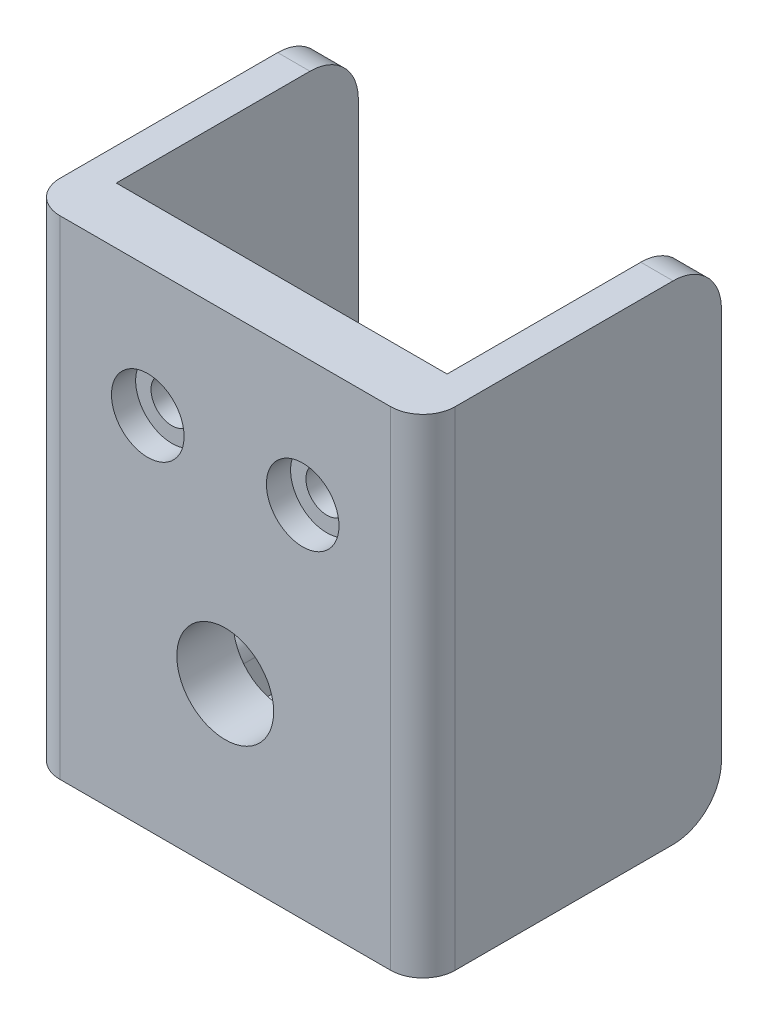
SolidWorks part; units mm, degrees
ref_plane "Front Plane" through (0, 0, 0) normal (0, 0, 1) x (1, 0, 0)
ref_plane "Top Plane" through (0, 0, 0) normal (0, 1, 0) x (1, 0, 0)
ref_plane "Right Plane" through (0, 0, 0) normal (1, 0, 0) x (0, 0, -1)
sketch "Sketch1" plane through (0, 0, 0) normal (0, 0, 1) x (1, 0, 0)
  line L0 (-10.25, 13) -> (10.25, 13)
  line L1 (-10.25, 13) -> (-10.25, -17.25)
  line L2 (-10.25, -17.25) -> (10.25, -17.25)
  line L3 (10.25, 13) -> (10.25, -17.25)
  line L4 (-4.8, 5) -> (4.8, 5) construction
  line L5 (0, -7) -> (0, -17.25) construction
  line L6 (0, 13) -> (0, 5) construction
  line L7 (0, 5) -> (0, 0) construction
  line L8 (0, 0) -> (0, -7) construction
  circle A1 centre (-4.8, 5) radius 1.3
  circle A2 centre (4.8, 5) radius 1.3
  circle A3 centre (0, -7) radius 3
  point P14 (0, 5)
  dimension "D3" = 2.6
  dimension "D4" = 6
  dimension "D1" = 30.25
  dimension "D2" = 20.5
  dimension "D5" = 10.25
  dimension "D6" = 8
  dimension "D7" = 9.6
  dimension "D8" = 7
extrude "Boss-Extrude1" add sketch "Sketch1" along normal blind 3.5
sketch "Sketch2" plane through (0, -17.25, 0) normal (0, -1, 0) x (-1, 0, 0)
  line L1 (10.25, -3.5) -> (12.25, -3.5)
  line L2 (10.25, -3.5) -> (10.25, 15)
  line L3 (10.25, 15) -> (12.25, 15)
  line L4 (12.25, -3.5) -> (12.25, 15)
  line L5 (-10.25, -3.5) -> (-12.25, -3.5)
  line L6 (-10.25, -3.5) -> (-10.25, 15)
  line L7 (-10.25, 15) -> (-12.25, 15)
  line L8 (-12.25, -3.5) -> (-12.25, 15)
  dimension "D1" = 2
  dimension "D2" = 18.5
extrude "Boss-Extrude2" add sketch "Sketch2" against normal up to vertex (30.25 mm away)
sketch "Sketch3" plane through (0, -17.25, 0) normal (0, -1, 0) x (1, 0, 0)
  line L0 (0, 3.5) -> (0, 0) construction
  line L5 (-12.25, 3.5) -> (12.25, 3.5) construction
  line L6 (0, 0) -> (0, -15.097) construction
  line L11 (-3.75, -10.5) -> (3.75, -10.5) construction
  line L12 (-10.25, 0) -> (-3.75, 0)
  line L13 (-10.25, 0) -> (-10.25, -10.5)
  line L14 (-10.25, -10.5) -> (-3.75, -10.5)
  line L15 (-3.75, 0) -> (-3.75, -10.5)
  line L16 (10.25, 0) -> (3.75, 0)
  line L17 (10.25, 0) -> (10.25, -10.5)
  line L18 (10.25, -10.5) -> (3.75, -10.5)
  line L19 (3.75, 0) -> (3.75, -10.5)
  point P15 (0, -10.5)
  dimension "D1" = 10.5
  dimension "D3" = 7.5
extrude "Boss-Extrude3" add sketch "Sketch3" against normal blind 2
fillet "Fillet1" radius 3.5 2 edges at (3.75, -16.25, 0) (-3.75, -16.25, 0)
fillet "Fillet2" radius 2 2 edges at (-12.25, -2.125, 3.5) (12.25, -2.125, 3.5)
sketch "Sketch4" plane through (0, 0, 3.5) normal (0, 0, 1) x (1, 0, 0)
  circle A0 centre (-4.8, 5) radius 2.25
  circle A1 centre (4.8, 5) radius 2.25
  dimension "D1" = 4.5
extrude "Cut-Extrude1" cut sketch "Sketch4" against normal blind 1.5
fillet "Fillet4" radius 3 4 edges at (11.25, 13, -15) (-11.25, 13, -15) (-11.25, -17.25, -15) (11.25, -17.25, -15)
sketch "Sketch7" [suppressed] plane through (12.25, 0, 0) normal (1, 0, 0) x (0, 0, -1)
  line L0 (-1.0366, -17.25) -> (-1.0366, -7.25) construction
  line L1 (12, -17.25) -> (-1.5, -17.25) construction
  line L2 (0.7746, -7.25) -> (-1.0366, -7.25) construction
  line L4 (4.2746, -7.25) -> (16.1029, -7.25) construction
  line L5 (4.2746, -3.75) -> (16.1029, -3.75) construction
  line L6 (4.2746, -10.75) -> (16.1029, -10.75) construction
  arc A0 (4.2746, -3.75) -> (4.2746, -10.75) centre (4.2746, -7.25) ccw construction
  arc A1 (16.1029, -10.75) -> (16.1029, -3.75) centre (16.1029, -7.25) ccw construction
  point P9 (10.1887, -7.25)
  dimension "D1" = 3.5
  dimension "D2" = 10
extrude "Cut-Extrude4" [suppressed] cut sketch "Sketch7" against normal blind 10
fillet "Fillet5" [suppressed] radius 1.5
sketch "Sketch9" plane through (0, 0, 0) normal (0, 0, -1) x (-1, 0, 0)
  line L1 (-10.25, -15.25) -> (-6.25, -15.25)
  line L2 (-10.25, -15.25) -> (-10.25, -11.25)
  line L3 (-10.25, -11.25) -> (-6.25, -11.25)
  line L4 (-6.25, -15.25) -> (-6.25, -11.25)
  line L5 (10.25, -15.25) -> (6.25, -15.25)
  line L6 (10.25, -15.25) -> (10.25, -11.25)
  line L7 (10.25, -11.25) -> (6.25, -11.25)
  line L8 (6.25, -15.25) -> (6.25, -11.25)
  dimension "D1" = 4
extrude "Boss-Extrude4" add sketch "Sketch9" along normal blind 6.5
fillet "Fillet6" radius 1.5 6 edges at (-6.25, -11.25, -3.25) (6.25, -11.25, -3.25) (-10.25, -16.25, -10.5) (10.25, -16.25, -10.5) (-3.75, -16.25, -10.5) (3.75, -16.25, -10.5)
sketch "Sketch10" plane through (0, -17.25, 0) normal (0, -1, 0) x (1, 0, 0)
  line L0 (0, 0) -> (0, -3.3411) construction
  line L1 (-0.25, 0) -> (0.25, 0)
  line L3 (0, -3.3411) -> (0, -3.5) construction
  line L4 (-3.7464, -3.3411) -> (-1.9483, -3.3411)
  line L5 (-1.9483, -3.3411) -> (1.9483, -3.3411) construction
  line L6 (1.9483, -3.3411) -> (3.7464, -3.3411)
  arc A0 (-0.25, 0) -> (-3.7464, -3.3411) centre (-0.25, -3.5) ccw
  arc A1 (0.25, 0) -> (3.7464, -3.3411) centre (0.25, -3.5) cw
  circle A2 centre (0, -3.5) radius 1.9548 construction
  arc A4 (-1.9483, -3.3411) -> (1.9483, -3.3411) centre (0, -3.5) cw
extrude "Boss-Extrude5" add sketch "Sketch10" against normal blind 2
sketch "Sketch11" plane through (0, -17.25, 0) normal (0, -1, 0) x (1, 0, 0)
  line L0 (0, -1.5452) -> (0, -3.5) construction
  line L1 (-1.9483, -3.3411) -> (-3.7464, -3.3411)
  line L2 (1.9483, -3.3411) -> (3.7464, -3.3411)
  line L3 (0, 0) -> (0, -1.5452) construction
  circle A1 centre (0, -3.5) radius 3.7466 construction
  circle A2 centre (0, -3.5) radius 1.9548 construction
  arc A3 (-3.7464, -3.3411) -> (3.7464, -3.3411) centre (0, -3.5033) cw
  arc A4 (-1.9483, -3.3411) -> (1.9483, -3.3411) centre (0, -3.5) cw
extrude "Boss-Extrude6" add sketch "Sketch11" along normal blind 1
